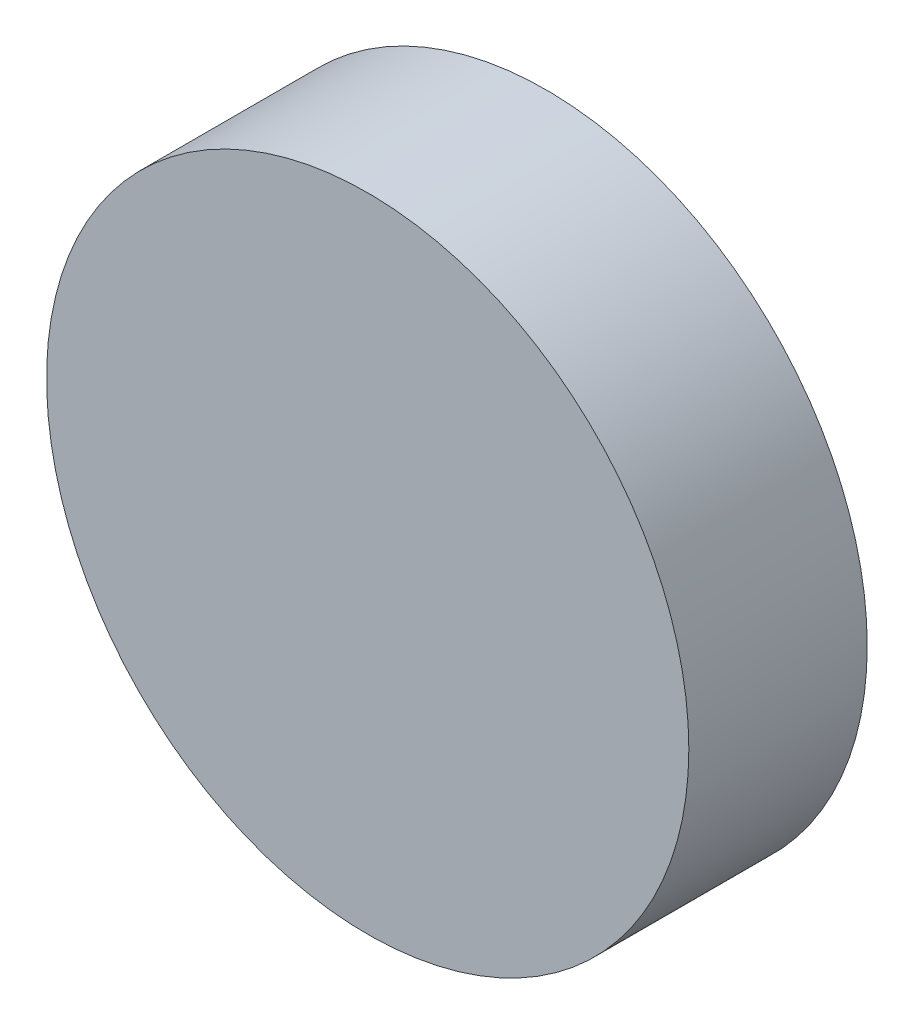
SolidWorks part; units mm, degrees
ref_plane "Front Plane" through (0, 0, 0) normal (0, 0, 1) x (1, 0, 0)
ref_plane "Top Plane" through (0, 0, 0) normal (0, 1, 0) x (1, 0, 0)
ref_plane "Right Plane" through (0, 0, 0) normal (1, 0, 0) x (0, 0, -1)
sketch "Sketch1" plane through (0, 0, 0) normal (0, 0, 1) x (1, 0, 0)
  circle A0 centre (0, 0) radius 228.6
  dimension "D1" = 457.2
extrude "Boss-Extrude1" add sketch "Sketch1" along normal blind 127
sketch "Sketch2" plane through (0, 0, 0) normal (0, 0, -1) x (-1, 0, 0)
  line L0 (-228.6, 0) -> (228.6, 0) construction
  line L1 (0, 228.6) -> (0, -228.6) construction
  circle A0 centre (0, 0) radius 228.6 construction
sketch "Sketch3" plane through (0, 0, 127) normal (0, 0, 1) x (1, 0, 0)
  line L0 (0, 228.6) -> (0, -228.6) construction
  line L1 (-228.6, 0) -> (228.6, 0) construction
  circle A0 centre (0, 0) radius 228.6 construction
